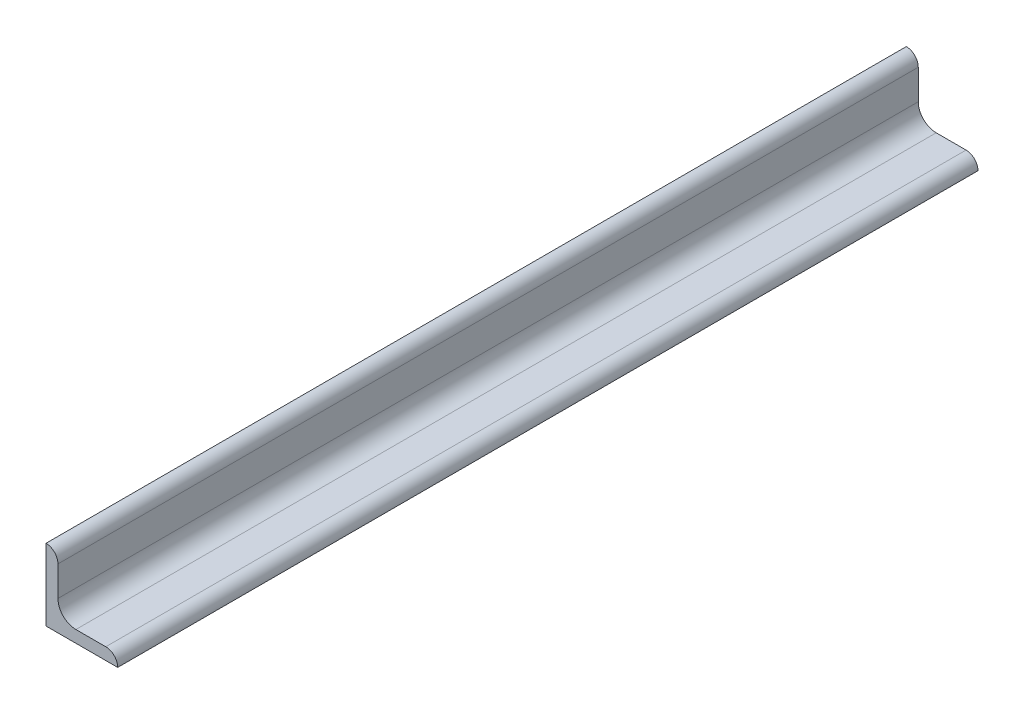
SolidWorks part; units mm, degrees
ref_plane "Plane1" through (0, 0, 0) normal (0, 0, 1) x (1, 0, 0)
ref_plane "Plane2" through (0, 0, 0) normal (0, 1, 0) x (1, 0, 0)
ref_plane "Plane3" through (0, 0, 0) normal (1, 0, 0) x (0, 0, -1)
sketch "Sketch1" plane through (0, 0, 0) normal (0, 0, 1) x (1, 0, 0)
  line L0 (0, 0) -> (0, 19.05)
  line L1 (0, 19.05) -> (0.0051, 19.05)
  line L2 (3.175, 15.8801) -> (3.175, 7.9375)
  line L3 (7.9375, 3.175) -> (15.8801, 3.175)
  line L4 (19.05, 0.0051) -> (19.05, 0)
  line L5 (19.05, 0) -> (0, 0)
  arc A0 (19.05, 0.0051) -> (15.8801, 3.175) centre (15.8801, 0.0051) ccw
  arc A1 (0.0051, 19.05) -> (3.175, 15.8801) centre (0.0051, 15.8801) cw
  arc A2 (7.9375, 3.175) -> (3.175, 7.9375) centre (7.9375, 7.9375) cw
  circle A3 centre (0, 0) radius 3.175 construction
  dimension "D2" = 0.0051
  dimension "Radius_1" = 4.7625
  dimension "Radius_2" = 3.175
  dimension "D1" = 3.175
  dimension "V_leg" = 19.05
  dimension "H_leg" = 19.05
  dimension "Thickness" = 3.175
  dimension "Flat_wid" = 0.0051
extrude "BaseSteelAngle" add sketch "Sketch1" along normal mid plane 228.6
equation "\"Flat_wid@Sketch1\" = ((sgn(\"Thickness@Sketch1\" - \"Radius_2@Sketch1\") +1)*(\"Thickness@Sketch1\" - \"Radius_2@Sketch1\"))/2 +0.0002"
equation "\"D1@Sketch1\" = \"Thickness@Sketch1\""
equation "\"D2@Sketch1\" = \"Flat_wid@Sketch1\""
